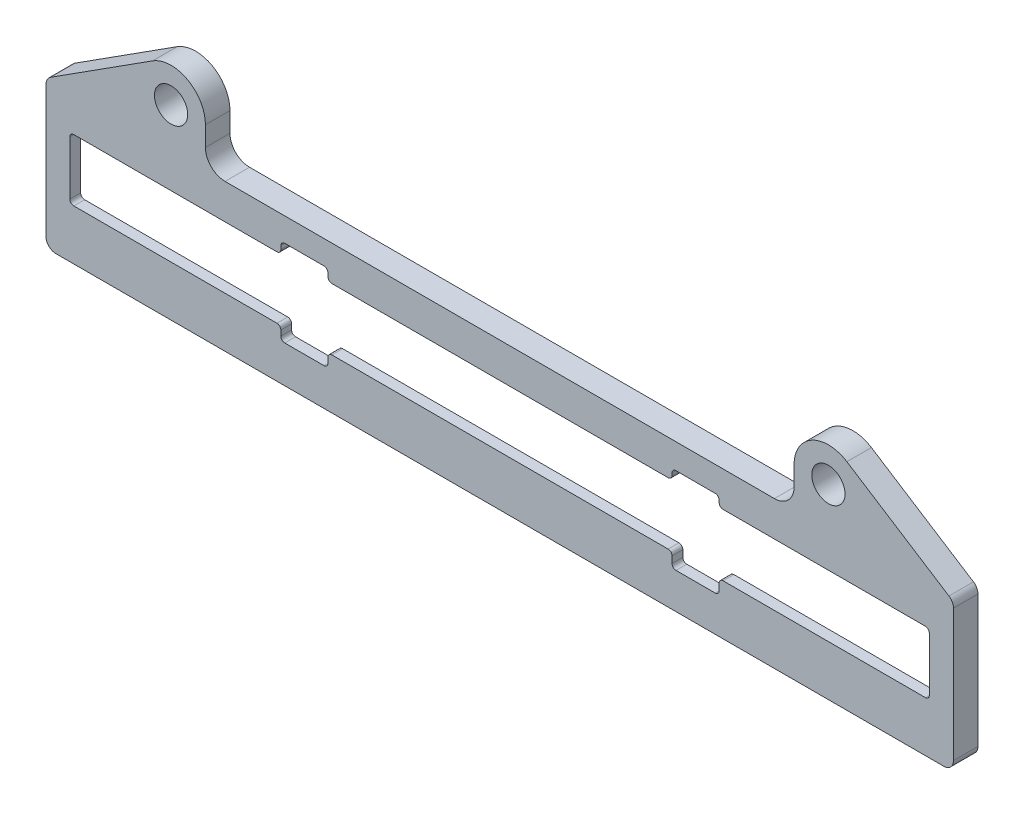
SolidWorks part; units mm, degrees
material "ABS PC"
ref_plane "Front Plane" through (0, 0, 0) normal (0, 0, 1) x (1, 0, 0)
ref_plane "Top Plane" through (0, 0, 0) normal (0, 1, 0) x (1, 0, 0)
ref_plane "Right Plane" through (0, 0, 0) normal (1, 0, 0) x (0, 0, -1)
sketch "Sketch1" plane through (0, 0, 0) normal (0, 0, 1) x (1, 0, 0)
  line L16 (58.7375, -67.1355) -> (58.7375, -48.0855)
  line L17 (58.7375, -48.0855) -> (44.94, -39.2609)
  line L18 (38.1, -43.0055) -> (38.1, -45.5455)
  line L19 (35.56, -48.0855) -> (-35.56, -48.0855)
  line L20 (-38.1, -45.5455) -> (-38.1, -43.0055)
  line L21 (-44.94, -39.2609) -> (-58.7375, -48.0855)
  line L22 (-58.7375, -48.0855) -> (-58.7375, -67.1355)
  line L23 (-58.7375, -67.1355) -> (58.7375, -67.1355)
  arc A8 (44.94, -39.2609) -> (38.1, -43.0055) centre (42.545, -43.0055) ccw
  arc A9 (35.56, -48.0855) -> (38.1, -45.5455) centre (35.56, -45.5455) ccw
  arc A10 (-38.1, -45.5455) -> (-35.56, -48.0855) centre (-35.56, -45.5455) ccw
  arc A11 (-38.1, -43.0055) -> (-44.94, -39.2609) centre (-42.545, -43.0055) ccw
extrude "Boss-Extrude1" add sketch "Sketch1" along normal blind 3.175
hole_wizard "#6 Clearance Hole1" positions "Sketch3" profile "Sketch2" hole size "#6" standard "ANSI Inch" end condition through all
sketch "Sketch3" plane through (0, 0, 0) normal (0, 0, -1) x (-1, 0, 0)
  point P0 (42.545, -43.0055)
  point P3 (-42.545, -43.0055)
sketch "Sketch2" plane through (-42.545, -43.0055, 0) normal (1, 0, 0) x (0, 1, 0)
  line L0 (0, 0) -> (0, 3.175)
  line L1 (0, 3.175) -> (2.1526, 3.175)
  line L2 (2.1526, 3.175) -> (2.1526, 0)
  line L5 (2.1526, 0) -> (0, 0)
  line L11 (0, -6.35) -> (0, 107.95) construction
  dimension "Thru Hole Dia." = 4.3053
  dimension "Thru Hole Depth" = 3.175
fillet "Fillet3" radius 1.27 4 edges at (58.7375, -67.1355, 1.5875) (58.7375, -48.0855, 1.5875) (-58.7375, -48.0855, 1.5875) (-58.7375, -67.1355, 1.5875)
sketch "Sketch4" [suppressed] plane through (0, 0, 4.7625) normal (0, 0, 1) x (1, 0, 0)
  line L0 (10.4267, -56.6199) -> (6.4267, -56.6199) construction
  line L1 (13.4667, -64.2399) -> (3.3867, -64.2399)
  line L2 (13.4667, -64.2399) -> (13.4667, -48.9999)
  line L3 (13.4667, -48.9999) -> (3.3867, -48.9999)
  line L4 (3.3867, -64.2399) -> (3.3867, -48.9999)
  line L5 (13.4667, -64.2399) -> (3.3867, -48.9999) construction
  line L6 (13.4667, -48.9999) -> (3.3867, -64.2399) construction
  line L7 (5.9267, -52.0399) -> (5.9267, -53.5799) construction
  line L8 (10.4267, -51.5399) -> (6.4267, -51.5399) construction
  point P0 (8.4267, -56.6199)
  dimension "D1" = 2.54
  dimension "D2" = 2.54
extrude "Cut-Extrude1" [suppressed] cut sketch "Sketch4" against normal through all
fillet "Fillet4" [suppressed] radius 2.54
sketch "Sketch7" [suppressed] plane through (0, 0, 0) normal (0, 0, -1) x (-1, 0, 0)
  line L0 (58.039, -60.8725) -> (58.039, -52.3672)
  line L1 (58.039, -52.3672) -> (55.0526, -49.3809)
  line L2 (55.0526, -49.3809) -> (-55.0526, -49.3809)
  line L3 (-55.0526, -49.3809) -> (-58.039, -52.3672)
  line L4 (-58.039, -52.3672) -> (-58.039, -60.8725)
  line L5 (-58.039, -60.8725) -> (-55.0526, -63.8589)
  line L6 (-55.0526, -63.8589) -> (55.0526, -63.8589)
  line L7 (55.0526, -63.8589) -> (58.039, -60.8725)
  line L8 (57.277, -60.5569) -> (57.277, -52.6829)
  line L9 (57.277, -52.6829) -> (54.737, -50.1429)
  line L10 (54.737, -50.1429) -> (-54.737, -50.1429)
  line L11 (-54.737, -50.1429) -> (-57.277, -52.6829)
  line L12 (-57.277, -52.6829) -> (-57.277, -60.5569)
  line L13 (-57.277, -60.5569) -> (-54.737, -63.0969)
  line L14 (-54.737, -63.0969) -> (54.737, -63.0969)
  line L15 (54.737, -63.0969) -> (57.277, -60.5569)
  line L16 (57.277, -60.5569) -> (57.277, -52.6829) construction
  line L17 (57.277, -52.6829) -> (54.737, -50.1429) construction
  line L18 (54.737, -50.1429) -> (-54.737, -50.1429) construction
  line L19 (-54.737, -50.1429) -> (-57.277, -52.6829) construction
  line L20 (-57.277, -52.6829) -> (-57.277, -60.5569) construction
  line L21 (-57.277, -60.5569) -> (-54.737, -63.0969) construction
  line L22 (-54.737, -63.0969) -> (54.737, -63.0969) construction
  line L23 (54.737, -63.0969) -> (57.277, -60.5569) construction
  dimension "D1" = 0
  dimension "D2" = 0.762
extrude "Cut-Extrude2" [suppressed] cut sketch "Sketch7" against normal blind 1.524
sketch "Sketch5" [suppressed] plane through (0, 0, 0) normal (0, 0, -1) x (-1, 0, 0)
  line L0 (-57.277, -52.6829) -> (-54.737, -50.1429) construction
  line L1 (-55.8146, -50.1429) -> (-57.277, -50.1429)
  line L2 (-57.277, -50.1429) -> (-57.277, -51.6052)
  line L3 (-57.277, -60.5569) -> (-54.737, -63.0969) construction
  line L4 (-57.277, -60.5569) -> (-54.737, -63.0969) construction
  line L5 (-55.8146, -63.0969) -> (-57.277, -63.0969)
  line L6 (-57.277, -63.0969) -> (-57.277, -61.6345)
  line L7 (54.737, -63.0969) -> (57.277, -60.5569) construction
  line L8 (57.277, -61.6345) -> (57.277, -63.0969)
  line L9 (57.277, -63.0969) -> (55.8146, -63.0969)
  line L10 (57.277, -52.6829) -> (54.737, -50.1429) construction
  line L11 (-54.737, -50.1429) -> (54.737, -50.1429) construction
  line L12 (55.8146, -50.1429) -> (57.277, -50.1429)
  line L13 (57.277, -50.1429) -> (57.277, -51.6052)
  line L14 (-57.277, -51.6052) -> (-55.8146, -50.1429)
  line L15 (-57.277, -61.6345) -> (-55.8146, -63.0969)
  line L16 (55.8146, -63.0969) -> (57.277, -61.6345)
  line L17 (57.277, -51.6052) -> (55.8146, -50.1429)
  line L18 (57.8158, -52.1441) -> (55.2758, -49.6041) construction
  line L19 (55.2758, -63.6357) -> (57.8158, -61.0957) construction
  line L20 (-57.8158, -61.0957) -> (-55.2758, -63.6357) construction
  line L21 (-57.8158, -52.1441) -> (-55.2758, -49.6041) construction
  dimension "D1" = 0.762
  dimension "D2" = 0.762
extrude "Boss-Extrude2" [suppressed] add sketch "Sketch5" along normal blind 1.524
sketch "Sketch8" plane through (0, 0, 0) normal (0, 0, -1) x (-1, 0, 0)
  line L8 (58.028, -61.8743) -> (58.028, -51.3743)
  line L9 (55.52, -48.8663) -> (-55.48, -48.8663)
  line L10 (-57.988, -51.3743) -> (-57.988, -61.8743)
  line L11 (-55.48, -64.3823) -> (55.52, -64.3823)
  line L12 (58.028, -61.8743) -> (58.028, -51.3743)
  line L13 (55.52, -48.8663) -> (-55.48, -48.8663)
  line L14 (-57.988, -51.3743) -> (-57.988, -61.8743)
  line L15 (-55.48, -64.3823) -> (55.52, -64.3823)
  arc A8 (58.028, -51.3743) -> (55.52, -48.8663) centre (55.52, -51.3743) ccw
  arc A9 (-55.48, -48.8663) -> (-57.988, -51.3743) centre (-55.48, -51.3743) ccw
  arc A10 (-57.988, -61.8743) -> (-55.48, -64.3823) centre (-55.48, -61.8743) ccw
  arc A11 (55.52, -64.3823) -> (58.028, -61.8743) centre (55.52, -61.8743) ccw
  arc A12 (58.028, -51.3743) -> (55.52, -48.8663) centre (55.52, -51.3743) ccw
  arc A13 (-55.48, -48.8663) -> (-57.988, -51.3743) centre (-55.48, -51.3743) ccw
  arc A14 (-57.988, -61.8743) -> (-55.48, -64.3823) centre (-55.48, -61.8743) ccw
  arc A15 (55.52, -64.3823) -> (58.028, -61.8743) centre (55.52, -61.8743) ccw
  dimension "D1" = 0.508
extrude "Cut-Extrude3" cut sketch "Sketch8" against normal blind 1.778
sketch "Sketch9" plane through (0, 0, 3.175) normal (0, 0, 1) x (1, 0, 0)
  line L0 (-27.576, -56.7474) -> (-23.004, -56.7474) construction
  line L1 (-23.004, -51.6674) -> (-27.576, -51.6674) construction
  line L2 (-28.338, -62.3354) -> (-22.242, -62.3354)
  line L3 (-28.338, -62.3354) -> (-28.338, -51.1594)
  line L4 (-28.338, -51.1594) -> (-22.242, -51.1594)
  line L5 (-22.242, -62.3354) -> (-22.242, -51.1594)
  line L6 (-28.338, -62.3354) -> (-22.242, -51.1594) construction
  line L7 (-28.338, -51.1594) -> (-22.242, -62.3354) construction
  line L8 (-22.75, -53.9534) -> (-22.75, -51.9214) construction
  line L9 (23.069, -56.9193) -> (27.641, -56.9193) construction
  line L11 (22.307, -51.3313) -> (28.403, -51.3313)
  line L12 (22.307, -51.3313) -> (22.307, -62.5073)
  line L13 (22.307, -62.5073) -> (28.403, -62.5073)
  line L14 (28.403, -51.3313) -> (28.403, -62.5073)
  line L15 (22.307, -51.3313) -> (28.403, -62.5073) construction
  line L16 (22.307, -62.5073) -> (28.403, -51.3313) construction
  point P4 (-25.29, -56.7474)
  point P17 (25.355, -56.9193)
  dimension "D1" = 0.508
  dimension "D2" = 0.508
extrude "Cut-Extrude4" cut sketch "Sketch9" against normal through all
sketch "Sketch10" plane through (0, 0, 1.778) normal (0, 0, -1) x (-1, 0, 0)
  line L0 (0.02, -64.3823) -> (0.02, -48.8663) construction
  line L1 (-55.48, -64.3823) -> (55.52, -64.3823) construction
  line L2 (55.52, -48.8663) -> (-55.48, -48.8663) construction
  line L4 (55.6467, -60.6243) -> (-55.6068, -60.6243)
  line L5 (55.6467, -60.6243) -> (55.6467, -52.6243)
  line L6 (55.6467, -52.6243) -> (-55.6068, -52.6243)
  line L7 (-55.6068, -60.6243) -> (-55.6068, -52.6243)
  line L8 (55.6467, -60.6243) -> (-55.6068, -52.6243) construction
  line L9 (55.6467, -52.6243) -> (-55.6068, -60.6243) construction
  line L10 (-57.988, -51.3743) -> (-57.988, -61.8743) construction
  point P6 (0.02, -56.6243)
  dimension "D1" = 8
  dimension "D2" = 2.3812
extrude "Cut-Extrude5" cut sketch "Sketch10" against normal through all
fillet "Fillet5" radius 0.508 20 edges at (-22.242, -62.3354, 2.4765) (-28.338, -51.1594, 2.4765) (-22.242, -51.1594, 2.4765) (-28.338, -62.3354, 2.4765) (22.307, -62.5073, 2.4765) (22.307, -51.3313, 2.4765) (28.403, -51.3313, 2.4765) (28.403, -62.5073, 2.4765) (-22.242, -52.6243, 2.4765) (-28.338, -52.6243, 2.4765) (-55.6467, -60.6243, 2.4765) (-28.338, -60.6243, 2.4765) (-22.242, -60.6243, 2.4765) (22.307, -60.6243, 2.4765) (28.403, -60.6243, 2.4765) (55.6068, -60.6243, 2.4765) (55.6068, -52.6243, 2.4765) (28.403, -52.6243, 2.4765) (22.307, -52.6243, 2.4765) (-55.6467, -52.6243, 2.4765)
